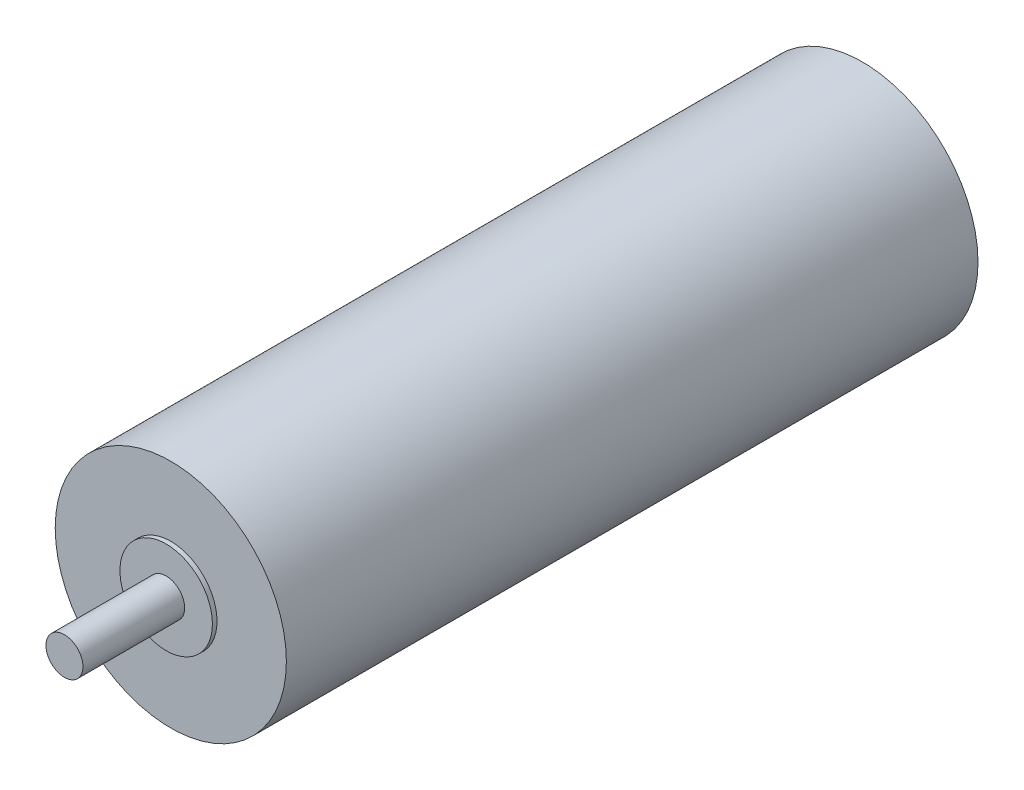
SolidWorks part; units mm, degrees
ref_plane "Front Plane" through (0, 0, 0) normal (0, 0, 1) x (1, 0, 0)
ref_plane "Top Plane" through (0, 0, 0) normal (0, 1, 0) x (1, 0, 0)
ref_plane "Right Plane" through (0, 0, 0) normal (1, 0, 0) x (0, 0, -1)
sketch "Sketch3" plane through (0, 0, 0) normal (0, 0, 1) x (1, 0, 0)
  circle A2 centre (0, 0) radius 12.5
  dimension "D1" = 25
extrude "Boss-Extrude1" add sketch "Sketch3" along normal blind 74.8 contours A2
sketch "Sketch4" plane through (0, 0, 74.8) normal (0, 0, 1) x (1, 0, 0)
  circle A0 centre (0, 0) radius 5
  dimension "D1" = 10
extrude "Boss-Extrude2" add sketch "Sketch4" along normal blind 0.5
sketch "Sketch5" plane through (0, 0, 75.3) normal (0, 0, 1) x (1, 0, 0)
  circle A0 centre (0, 0) radius 2
  dimension "D1" = 4
extrude "Boss-Extrude3" add sketch "Sketch5" along normal blind 11
